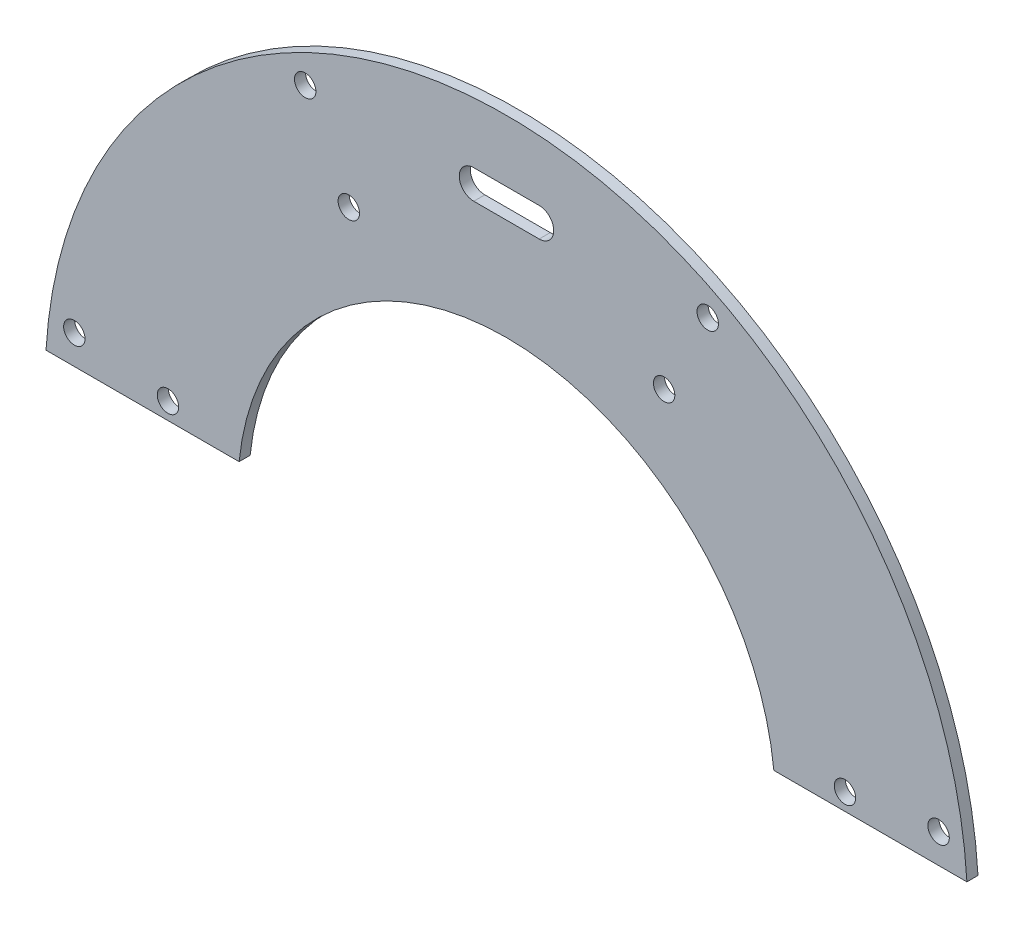
SolidWorks part; units mm, degrees
material "cirlex"
ref_plane "Front Plane" through (0, 0, 0) normal (0, 0, 1) x (1, 0, 0)
ref_plane "Top Plane" through (0, 0, 0) normal (0, 1, 0) x (1, 0, 0)
ref_plane "Right Plane" through (0, 0, 0) normal (1, 0, 0) x (0, 0, -1)
sketch "Sketch1" plane through (0, 0, 0) normal (0, 0, 1) x (1, 0, 0)
  line L2 (-63.3862, 3.8) -> (-36.8043, 3.8)
  line L3 (36.8043, 3.8) -> (63.3862, 3.8)
  line L4 (0, 0) -> (-15.1482, 0) construction
  arc A0 (63.3862, 3.8) -> (-63.3862, 3.8) centre (0, 0) ccw
  arc A1 (-36.8043, 3.8) -> (36.8043, 3.8) centre (0, 0) cw
  dimension "D1" = 63.5
  dimension "D2" = 37
  dimension "D3" = 3.8
extrude "Boss-Extrude1" add sketch "Sketch1" along normal mid plane 1.524
hole_wizard "#4 Clearance Hole1" positions "Sketch3" profile "Sketch2" hole size "#4" standard "ANSI Inch"
sketch "Sketch3" plane through (0, 0, 0.762) normal (0, 0, 1) x (1, 0, 0)
  line L0 (0, 0) -> (-33.3209, 0) construction
  line L1 (0, 0) -> (-29.1385, 3.8362) construction
  point P0 (-59.4867, 7.8316)
  point P9 (-46.5979, 6.1347)
  dimension "D1" = 7.5
  dimension "D2" = 60
  dimension "D3" = 47
sketch "Sketch2" plane through (-59.4867, 7.8316, 0.762) normal (1, 0, 0) x (0, -1, 0)
  line L0 (0, 0) -> (0, 136.7752)
  line L1 (0, 136.7752) -> (1.4732, 135.89)
  line L2 (1.4732, 135.89) -> (1.4732, 0)
  line L5 (1.4732, 0) -> (0, 0)
  line L10 (0, 136.7752) -> (-1.4732, 135.89) construction
  line L11 (0, -6.35) -> (0, 107.95) construction
  dimension "Hole Dia." = 2.9464
  dimension "Hole Depth" = 135.89
  dimension "Drill Angle" = 118
pattern_circular "CirPattern1" count 4 every 55 about axis through (0, 0, 0) along (0, 0, 1) of "#4 Clearance Hole1"
sketch "Sketch4" plane through (0, 0, 0.762) normal (0, 0, 1) x (1, 0, 0)
  line L0 (0, 0) -> (0, 21.4454) construction
  line L1 (-4.5, 53) -> (4.5, 53) construction
  line L2 (-4.5, 55) -> (4.5, 55)
  line L3 (-4.5, 51) -> (4.5, 51)
  line L4 (0, 0) -> (-12.7527, 0) construction
  circle A0 centre (0, 0) radius 50 construction
  circle A1 centre (0, 0) radius 56 construction
  arc A2 (-4.5, 55) -> (-4.5, 51) centre (-4.5, 53) ccw
  arc A3 (4.5, 51) -> (4.5, 55) centre (4.5, 53) ccw
  point P7 (0, 53)
  dimension "D1" = 112
  dimension "D2" = 100
  dimension "D3" = 53
  dimension "D4" = 4
  dimension "D5" = 9
extrude "Cut-Extrude1" cut sketch "Sketch4" against normal through all
